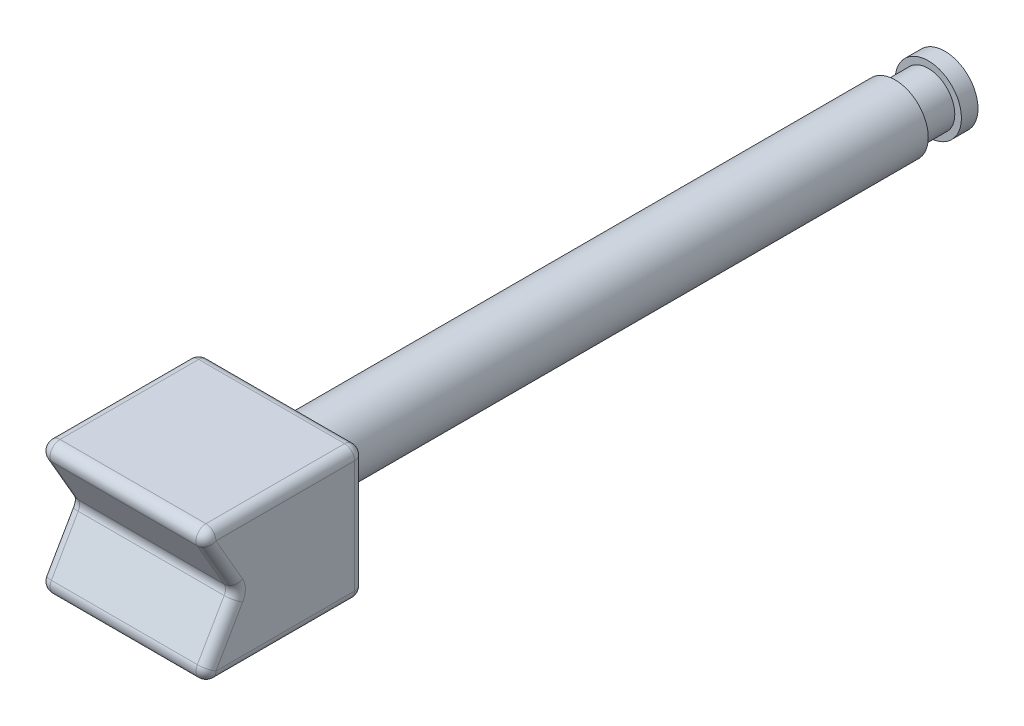
SolidWorks part; units mm, degrees
ref_plane "Plan de face" through (0, 0, 0) normal (0, 0, 1) x (1, 0, 0)
ref_plane "Plan de dessus" through (0, 0, 0) normal (0, 1, 0) x (1, 0, 0)
ref_plane "Plan de droite" through (0, 0, 0) normal (1, 0, 0) x (0, 0, -1)
sketch "Esquisse1" plane through (0, 0, 0) normal (0, 1, 0) x (1, 0, 0)
  line L0 (-2.75, 0) -> (2.75, 0) construction
  line L1 (-2.5, -2.5) -> (2.5, -2.5)
  line L2 (-2.5, -2.5) -> (-2.5, 2.5)
  line L3 (-2.5, 2.5) -> (2.5, 2.5)
  line L4 (2.5, -2.5) -> (2.5, 2.5)
  line L5 (-2.5, -2.5) -> (2.5, 2.5) construction
  line L6 (-2.5, 2.5) -> (2.5, -2.5) construction
  line L7 (0, -5.5) -> (0, 5.5) construction
  point P0 (0, 0)
  dimension "D1" = 5
  dimension "D2" = 5
extrude "Boss.-Extru.1" add sketch "Esquisse1" along normal mid plane 4
sketch "Esquisse2" plane through (-2.5, 0, 0) normal (-1, 0, 0) x (0, 0, 1)
  line L3 (2.5, 2) -> (1.3453, 0)
  line L4 (1.3453, 0) -> (2.5, -2)
  line L5 (2.5, -2) -> (2.5, 2)
  line L6 (2.5, 0) -> (-2.5, 0) construction
  line L7 (-2.5, 2) -> (-2.5, -2) construction
  dimension "D1" = 120
extrude "Enlèv. mat.-Extru.1" cut sketch "Esquisse2" against normal through all
sketch "Esquisse3" plane through (0, 0, -2.5) normal (0, 0, -1) x (-1, 0, 0)
  line L0 (0, 1.155) -> (0, -1.155) construction
  line L1 (2.75, 0) -> (-2.75, 0) construction
  circle A0 centre (0, 0) radius 1
  dimension "D1" = 2
extrude "Boss.-Extru.2" add sketch "Esquisse3" along normal blind 20
sketch "Esquisse4" plane through (0, 0, 0) normal (1, 0, 0) x (0, 0, -1)
  line L0 (22.5, 1) -> (2.5, 1) construction
  line L1 (21, 1) -> (22, 1)
  line L2 (21, 1) -> (21, 0.8)
  line L3 (21, 0.8) -> (22, 0.8)
  line L4 (22, 1) -> (22, 0.8)
  line L5 (22.5, -1) -> (22.5, 1) construction
  line L6 (23.5, 0) -> (24.5, 0) construction
  line L7 (2.75, 0) -> (-2.75, 0) construction
  point P6 (22, 0.9)
  dimension "D1" = 1
  dimension "D2" = 0.5
  dimension "D3" = 0.2
revolve "Enlèvement de matière-Révolution1" cut sketch "Esquisse4" angle 360 about L6
fillet "Congé3" radius 0.3 16 edges at (-2.5, 2, 0) (0, 2, 2.5) (2.5, -1, 1.9226) (2.5, 1, 1.9226) (0, 0, 1.3453) (-2.5, 1, 1.9226) (-2.5, -1, 1.9226) (-1, 0, -2.5) (2.5, 2, 0) (0, -2, 2.5) (-2.5, -2, 0) (0, -2, -2.5) (2.5, -2, 0) (-2.5, 0, -2.5) (2.5, 0, -2.5) (0, 2, -2.5)
